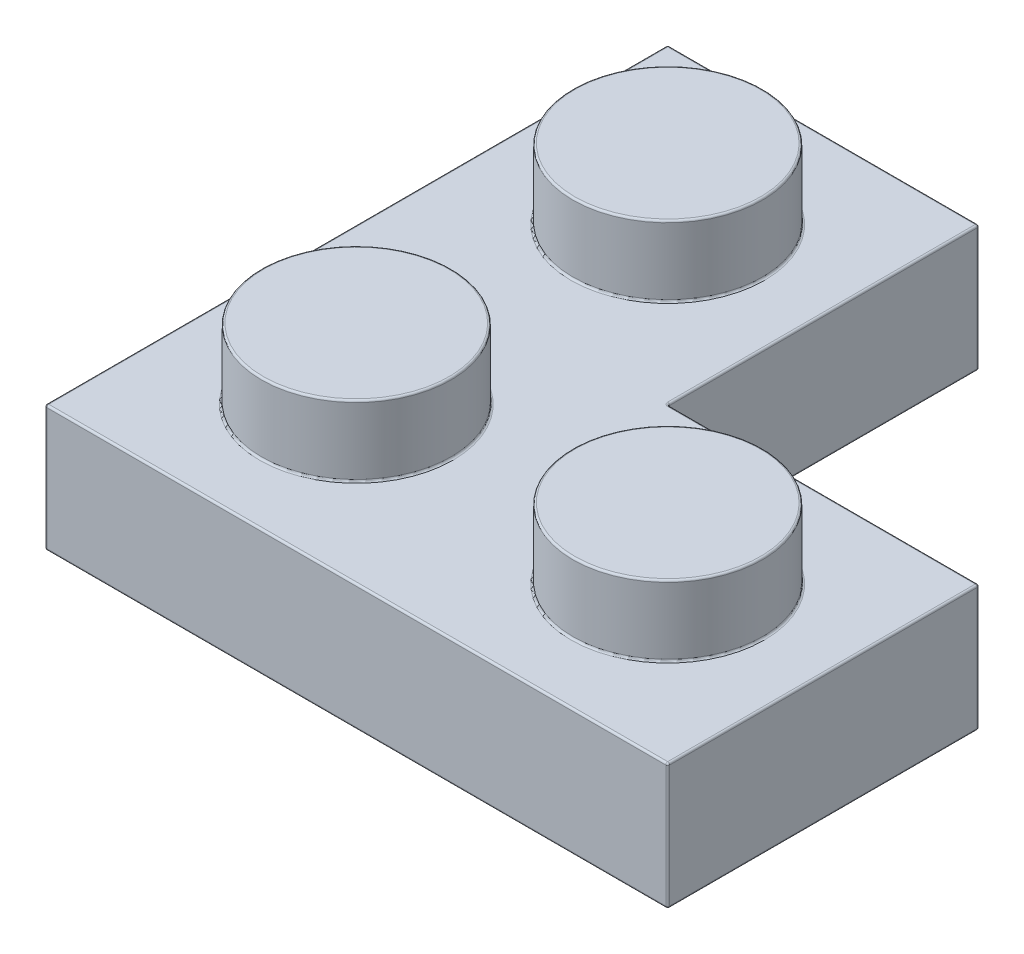
SolidWorks part; units mm, degrees
ref_plane "Front Plane" through (0, 0, 0) normal (0, 0, 1) x (1, 0, 0)
ref_plane "Top Plane" through (0, 0, 0) normal (0, 1, 0) x (1, 0, 0)
ref_plane "Right Plane" through (0, 0, 0) normal (1, 0, 0) x (0, 0, -1)
sketch "Sketch1" plane through (0, 0, 0) normal (0, 1, 0) x (1, 0, 0)
  line L1 (-3.98, 3.98) -> (3.98, 3.98)
  line L2 (-3.98, 3.98) -> (-3.98, -3.98)
  line L3 (-3.98, -3.98) -> (3.98, -3.98)
  line L4 (3.98, 3.98) -> (3.98, -3.98)
  line L5 (-3.98, 3.98) -> (3.98, -3.98) construction
  line L6 (-3.98, -3.98) -> (3.98, 3.98) construction
  point P0 (0, 0)
  dimension "D1" = 7.96
extrude "Extrude1" add sketch "Sketch1" along normal blind 3.22
sketch "Sketch2" plane through (0, 3.22, 0) normal (0, 1, 0) x (1, 0, 0)
  circle A0 centre (0, 0) radius 2.425
  dimension "D1" = 4.85
extrude "Extrude2" add sketch "Sketch2" along normal blind 1.8
pattern_linear "LPattern1" count 2 spacing 7.96 along (1, 0, 0) of "Extrude2", "Extrude1"
pattern_linear "LPattern2" count 2 spacing 7.96 along (0, 0, -1) of "Extrude1", "Extrude2"
shell "Shell1" thickness 1.55
sketch "Sketch4" plane through (0, 1.67, 0) normal (0, -1, 0) x (1, 0, 0)
  line L0 (2.43, -10.39) -> (-2.43, -10.39) construction
  line L1 (10.39, 2.43) -> (10.39, -2.43) construction
  line L2 (-2.43, 2.43) -> (10.39, 2.43) construction
  line L3 (-2.43, -10.39) -> (-2.43, 2.43) construction
  line L4 (10.39, -2.43) -> (2.43, -2.43) construction
  line L5 (2.43, -2.43) -> (2.43, -10.39) construction
  line L6 (2.43, -10.39) -> (-2.43, -10.39)
  line L7 (10.39, 2.43) -> (10.39, -2.43)
  line L8 (-2.43, 2.43) -> (10.39, 2.43)
  line L9 (-2.43, -10.39) -> (-2.43, 2.43)
  line L10 (10.39, -2.43) -> (2.43, -2.43)
  line L11 (2.43, -2.43) -> (2.43, -10.39)
extrude "Extrude3" cut sketch "Sketch4" against normal blind 0.14
sketch "Sketch5" plane through (0, 1.81, 0) normal (0, -1, 0) x (1, 0, 0)
  line L0 (-2.43, 2.43) -> (-2.43, -10.39) construction
  line L1 (-2.43, 2.43) -> (10.39, 2.43) construction
  circle A0 centre (0, -3.98) radius 1.5
  circle A1 centre (0, -3.98) radius 0.64
  circle A2 centre (3.98, 0) radius 1.5
  circle A3 centre (3.98, 0) radius 0.64
  point P9 (-2.43, -3.98)
  point P12 (3.98, 2.43)
  dimension "D1" = 3
  dimension "D2" = 0.86
extrude "Extrude4" add sketch "Sketch5" along normal up to surface (1.81 mm away) up to face at (3.4633, 0, -3.4633)
sketch "Sketch6" plane through (0, 1.81, 0) normal (0, -1, 0) x (1, 0, 0)
  line L0 (-2.43, 2.43) -> (2.43, -2.43) construction
  line L1 (2.43, -3.1795) -> (1.4542, -2.2037)
  line L2 (2.43, -10.39) -> (2.43, -2.43) construction
  line L3 (1.4542, -2.2037) -> (2.2037, -1.4542)
  line L4 (2.2037, -1.4542) -> (3.1795, -2.43)
  line L5 (2.43, -2.43) -> (10.39, -2.43) construction
  line L6 (10.39, -2.43) -> (2.43, -2.43) construction
  line L7 (2.43, -2.43) -> (2.43, -10.39) construction
  line L8 (3.1795, -2.43) -> (2.43, -2.43)
  line L9 (2.43, -2.43) -> (2.43, -3.1795)
  dimension "D1" = 1.38
  dimension "D2" = 1.06
extrude "Extrude5" add sketch "Sketch6" along normal up to surface (1.81 mm away) up to face at (3.4633, 0, -3.4633)
fillet "Fillet1" radius 0.05 65 edges at (2.6916, 1.81, -1.9421) (1.829, 1.81, -1.829) (1.9421, 1.81, -2.6916) (2.43, 0.905, -3.1795) (1.4542, 0.905, -2.2037) (2.2037, 0.905, -1.4542) (3.1795, 0.905, -2.43) (1.9421, 0, -2.6916) (1.829, 0, -1.829) (2.6916, 0, -1.9421) (3.98, 1.81, -0.64) (3.98, 0, 1.5) (3.98, 0, 0.64) (0, 1.81, -4.62) (0, 0, -2.48) (0, 0, -3.34) (2.43, 1.81, -6.7848) (6.7848, 1.81, -2.43) (10.39, 1.81, 0) (3.98, 1.81, 2.43) (-2.43, 1.81, -3.98) (0, 1.81, -10.39) (0, 1.81, -7.085) (7.96, 1.81, 0.875) (0, 1.81, 0.875) (0, 3.47, -7.085) (2.43, 0, -6.7848) (0, 0, -10.39) (-2.43, 0.905, -10.39) (2.43, 0.905, -10.39) (7.96, 3.47, 0.875) (10.39, 0, 0) (10.39, 0.905, 2.43) (10.39, 0.905, -2.43) (0, 3.47, 0.875) (6.7848, 0, -2.43) (-2.43, 0, -3.98) (3.98, 0, 2.43) (-2.43, 0.905, 2.43) (0, 3.22, -5.535) (0, 5.02, -5.535) (0, 0, -11.94) (0, 3.22, -11.94) (-3.98, 1.61, -11.94) (3.98, 1.61, -11.94) (7.96, 3.22, 2.425) (7.96, 5.02, 2.425) (11.94, 0, 0) (11.94, 3.22, 0) (11.94, 1.61, -3.98) (11.94, 1.61, 3.98) (0, 3.22, 2.425) (0, 5.02, 2.425) (-3.98, 0, -3.98) (3.98, 0, 3.98) (-3.98, 3.22, -3.98) (3.98, 3.22, 3.98) (-3.98, 1.61, 3.98) (0, 1.81, -2.48) (3.98, 1.81, 1.5)
